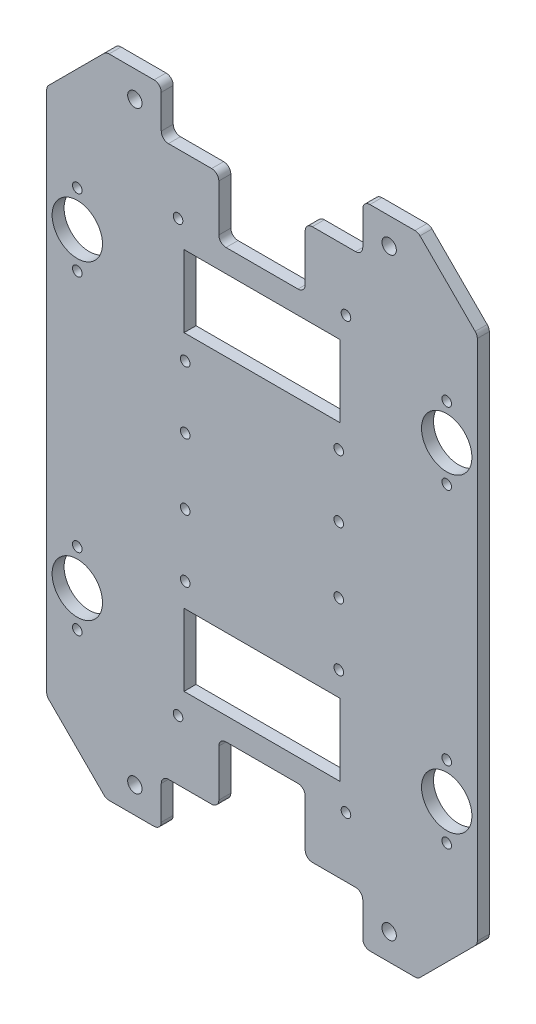
SolidWorks part; units mm, degrees
material "Alliage 1060"
ref_plane "Plan de dessus" through (0, 0, 0) normal (0, 0, 1) x (1, 0, 0)
ref_plane "Plan de droite" through (0, 0, 0) normal (0, 1, 0) x (1, 0, 0)
ref_plane "Plan de face" through (0, 0, 0) normal (1, 0, 0) x (0, 0, -1)
sketch "Esquisse1" plane through (0, 0, 0) normal (0, 0, 1) x (1, 0, 0)
  line L0 (0, 0) -> (-130, 0)
  line L1 (-130, 0) -> (-154.7487, 24.7487)
  line L2 (-154.7487, 24.7487) -> (-154.7487, 244.7487)
  line L3 (-154.7487, 244.7487) -> (-130, 269.4975)
  line L4 (-130, 269.4975) -> (0, 269.4975)
  line L5 (0, 269.4975) -> (24.7487, 244.7487)
  line L6 (24.7487, 244.7487) -> (24.7487, 24.7487)
  line L7 (24.7487, 24.7487) -> (0, 0)
  dimension "D1" = 220
  dimension "D2" = 35
  dimension "D3" = 135
  dimension "D4" = 130
extrude "Base" add sketch "Esquisse1" along normal blind 5
sketch "Esquisse3" plane through (0, 0, 0) normal (0, 0, -1) x (-1, 0, 0)
  line L0 (107, 0) -> (107, 20)
  line L1 (130, 0) -> (0, 0) construction
  line L2 (107, 20) -> (83, 20)
  line L3 (83, 20) -> (83, 45.5)
  line L4 (83, 45.5) -> (47, 45.5)
  line L5 (47, 45.5) -> (47, 20)
  line L6 (47, 20) -> (23, 20)
  line L7 (23, 20) -> (23, 0)
  line L8 (-24.7487, 134.7487) -> (154.7487, 134.7487) construction
  line L9 (-24.7487, 24.7487) -> (-24.7487, 244.7487) construction
  line L10 (154.7487, 244.7487) -> (154.7487, 24.7487) construction
  line L11 (23, 0) -> (107, 0)
  line L12 (23, 269.4975) -> (107, 269.4975)
  line L13 (107, 269.4975) -> (107, 249.4975)
  line L14 (107, 249.4975) -> (83, 249.4975)
  line L15 (83, 249.4975) -> (83, 223.9975)
  line L16 (83, 223.9975) -> (47, 223.9975)
  line L17 (47, 223.9975) -> (47, 249.4975)
  line L18 (47, 249.4975) -> (23, 249.4975)
  line L19 (23, 249.4975) -> (23, 269.4975)
  line L20 (65, 45.5) -> (65, -49954.5) construction
  line L21 (0, 269.4975) -> (130, 269.4975) construction
  line L22 (32.5, 214.4975) -> (97.5, 214.4975)
  line L23 (32.5, 214.4975) -> (32.5, 184.4975)
  line L24 (32.5, 184.4975) -> (97.5, 184.4975)
  line L25 (97.5, 214.4975) -> (97.5, 184.4975)
  line L26 (97.5, 55) -> (97.5, 85)
  line L27 (32.5, 85) -> (97.5, 85)
  line L28 (32.5, 55) -> (97.5, 55)
  line L29 (32.5, 55) -> (32.5, 85)
  circle A0 centre (30, 45) radius 2
  circle A1 centre (100, 45) radius 2
  circle A2 centre (100, 224.4975) radius 2
  circle A3 centre (30, 224.4975) radius 2
  point P4 (65, 45.5)
  point P11 (65, 0)
  point P40 (65, 214.4975)
  dimension "D7" = 4
  dimension "D5" = 25
  dimension "D1" = 20
  dimension "D2" = 24
  dimension "D3" = 36
  dimension "D4" = 25.5
  dimension "D6" = 7
  dimension "D8" = 55
  dimension "D9" = 30
  dimension "D10" = 65
extrude "Enlèv. mat.-Extru.1" cut sketch "Esquisse3" against normal through all
fillet "Congé1" radius 3 24 edges at (-154.7487, 24.7487, 2.5) (24.7487, 24.7487, 2.5) (0, 0, 2.5) (-107, 20, 2.5) (-83, 45.5, 2.5) (-83, 20, 2.5) (-130, 0, 2.5) (-107, 0, 2.5) (-47, 45.5, 2.5) (-23, 20, 2.5) (-47, 20, 2.5) (-23, 0, 2.5) (24.7487, 244.7487, 2.5) (-107, 249.4975, 2.5) (-83, 223.9975, 2.5) (-154.7487, 244.7487, 2.5) (-130, 269.4975, 2.5) (-107, 269.4975, 2.5) (-83, 249.4975, 2.5) (-47, 223.9975, 2.5) (-23, 249.4975, 2.5) (-47, 249.4975, 2.5) (-23, 269.4975, 2.5) (0, 269.4975, 2.5)
sketch "Esquisse6" plane through (0, 0, 5) normal (0, 0, 1) x (1, 0, 0)
  line L0 (-142, 214.4975) -> (-142, 199.4975) construction
  line L1 (-107, 3) -> (-107, 17) construction
  line L2 (-65, 231.5685) -> (-65, -49768.4315) construction
  line L3 (-107, 252.4975) -> (-107, 266.4975) construction
  line L4 (-32.5, 184.4975) -> (-97.5, 184.4975) construction
  line L5 (-203.2843, 134.7487) -> (49796.7157, 134.7487) construction
  line L6 (-154.7487, 243.5061) -> (-154.7487, 25.9914) construction
  line L11 (-142, 85) -> (-142, 70) construction
  line L13 (-142, 70) -> (-142, 55) construction
  line L15 (-128.7574, 0) -> (-110, 0) construction
  line L18 (-110, 269.4975) -> (-128.7574, 269.4975) construction
  circle A25 centre (-142, 55) radius 2
  circle A26 centre (-142, 85) radius 2
  circle A27 centre (-142, 70) radius 10.5
  circle A28 centre (-142, 214.4975) radius 2
  circle A29 centre (-142, 184.4975) radius 2
  circle A30 centre (-142, 199.4975) radius 10.5
  circle A31 centre (12, 55) radius 2
  circle A32 centre (12, 184.4975) radius 2
  circle A33 centre (12, 214.4975) radius 2
  circle A34 centre (12, 85) radius 2
  circle A35 centre (12, 70) radius 10.5
  circle A36 centre (12, 199.4975) radius 10.5
  point P15 (-65, 184.4975)
  point P20 (-154.7487, 134.7487)
  dimension "D2" = 15
  dimension "D7" = 70
  dimension "D9" = 35
  dimension "D10" = 30
  dimension "D6" = 21
  dimension "D11" = 35
  dimension "D13" = 21
  dimension "D14" = 30
  dimension "D15" = 70
extrude "Perçage pour billes" cut sketch "Esquisse6" against normal up to next
sketch "Esquisse8" plane through (0, 0, 5) normal (0, 0, 1) x (1, 0, 0)
  line L0 (-65, 223.9975) -> (-65, 85) construction
  line L1 (-50, 223.9975) -> (-80, 223.9975) construction
  line L2 (-97.5, 85) -> (-32.5, 85) construction
  line L3 (-110, 269.4975) -> (-128.7574, 269.4975) construction
  line L4 (-107, 252.4975) -> (-107, 266.4975) construction
  line L5 (-128.7574, 0) -> (-110, 0) construction
  line L6 (-107, 3) -> (-107, 17) construction
  circle A0 centre (-118, 11) radius 3
  circle A1 centre (-118, 258.4975) radius 3
  circle A2 centre (-12, 258.4975) radius 3
  circle A3 centre (-12, 11) radius 3
  dimension "D1" = 11
  dimension "D2" = 11
  dimension "D3" = 6
  dimension "D4" = 11
  dimension "D5" = 11
  dimension "D6" = 6
extrude "Perçage pour profilé" cut sketch "Esquisse8" against normal up to next
sketch "Esquisse10" plane through (0, 0, 5) normal (0, 0, 1) x (1, 0, 0)
  line L0 (-154.7487, 243.5061) -> (-154.7487, 25.9914) construction
  line L2 (-32.5, 184.4975) -> (-97.5, 184.4975) construction
  line L3 (-65, 184.4975) -> (-65, 85) construction
  line L4 (-97.5, 85) -> (-32.5, 85) construction
  line L5 (-154.7487, 134.7487) -> (24.7487, 134.7487) construction
  line L6 (24.7487, 25.9914) -> (24.7487, 243.5061) construction
  circle A0 centre (-97, 174.4975) radius 2
  circle A1 centre (-97, 148.4975) radius 2
  circle A2 centre (-33, 148.4975) radius 2
  circle A3 centre (-33, 174.4975) radius 2
  circle A4 centre (-33, 121) radius 2
  circle A5 centre (-33, 95) radius 2
  circle A6 centre (-97, 121) radius 2
  circle A7 centre (-97, 95) radius 2
  dimension "D1" = 26
  dimension "D2" = 32
  dimension "D3" = 4
  dimension "D4" = 4
  dimension "D5" = 10
extrude "Enlèv. mat.-Extru.3" cut sketch "Esquisse10" against normal through all
